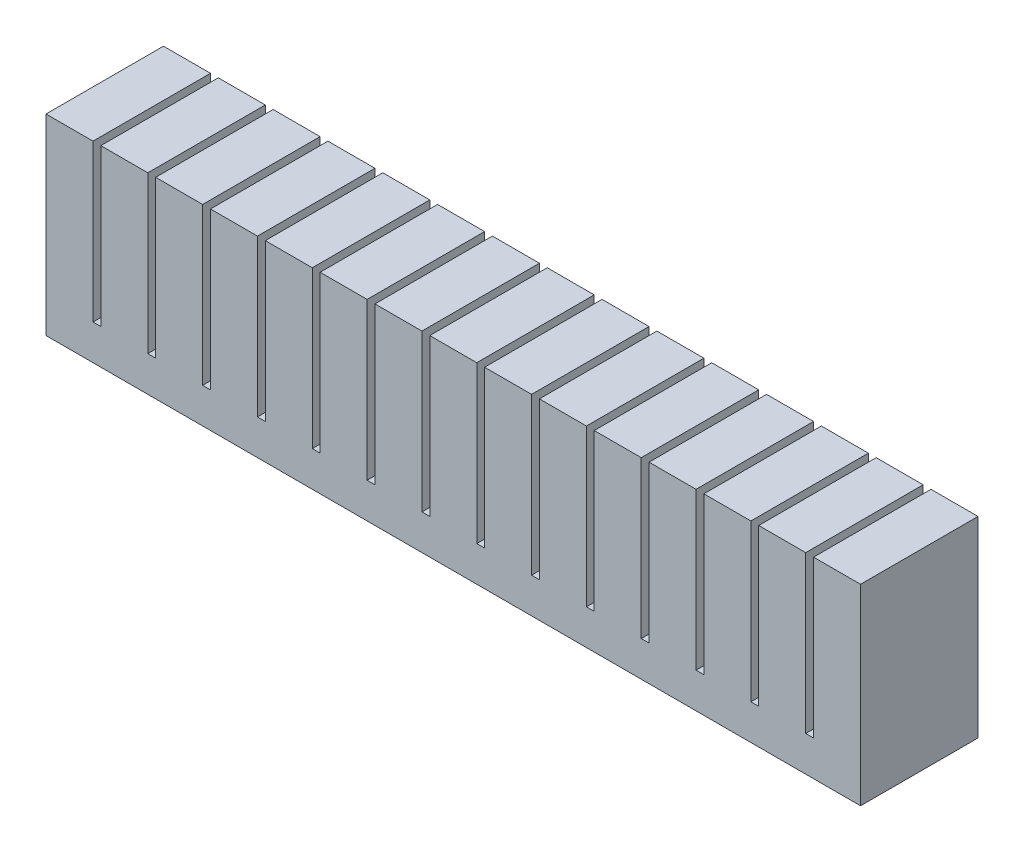
SolidWorks part; units mm, degrees
ref_plane "Front Plane" through (0, 0, 0) normal (0, 0, 1) x (1, 0, 0)
ref_plane "Top Plane" through (0, 0, 0) normal (0, 1, 0) x (1, 0, 0)
ref_plane "Right Plane" through (0, 0, 0) normal (1, 0, 0) x (0, 0, -1)
sketch "Sketch1" plane through (0, 0, 0) normal (0, 0, 1) x (1, 0, 0)
  line L0 (0, 0) -> (-3.5, 0)
  line L1 (-3.5, 0) -> (-3.5, 4.5)
  line L2 (-3.5, 4.5) -> (-3, 4.5)
  line L3 (-3, 4.5) -> (-3, 22.5)
  line L4 (-3, 22.5) -> (3, 22.5)
  line L5 (3, 22.5) -> (3, 4.5)
  line L6 (3, 4.5) -> (3.5, 4.5)
  line L7 (3.5, 4.5) -> (3.5, 0)
  line L8 (3.5, 0) -> (0, 0)
  point P12 (0, 22.5)
  dimension "D1" = 22.5
  dimension "D2" = 18
  dimension "D3" = 18
  dimension "D4" = 0.5
  dimension "D5" = 0.5
  dimension "D6" = 6
extrude "Boss-Extrude1" add sketch "Sketch1" along normal mid plane 15
pattern_linear "LPattern1" count 8 spacing 7 along (1, 0, 0) count 8 spacing 7 along (-1, 0, 0) of "Boss-Extrude1"
shell "Shell2" thickness 1
sketch "Sketch3" plane through (0, 0, 0) normal (0, 0, 1) x (1, 0, 0)
  line L0 (-52, 4.5) -> (-52.5, 4.5)
  line L1 (-52.5, 4.5) -> (-52.5, 0)
  line L2 (-52.5, 0) -> (52.5, 0) construction
  line L3 (-52.5, 4.5) -> (-52.5, 0) construction
  line L4 (-52.5, 0) -> (-52, 0)
  line L5 (-52, 0) -> (-52, 4.5)
  line L6 (52, 4.5) -> (52, 0)
  line L7 (52, 0) -> (52.5, 0)
  line L8 (52.5, 0) -> (52.5, 4.5)
  line L9 (52.5, 4.5) -> (52, 4.5)
extrude "Cut-Extrude2" cut sketch "Sketch3" along normal blind 15 and the other way through all
sketch "Sketch7" plane through (-52, 0, 0) normal (-1, 0, 0) x (0, 0, 1)
  line L0 (7.5, 22.5) -> (7.5, 0) construction
  line L1 (0, 0) -> (7.5, 0)
  line L2 (0, 0) -> (0, 1)
  line L3 (0, 1) -> (7.5, 1)
  line L4 (7.5, 0) -> (7.5, 1)
  dimension "D1" = 1
extrude "Cut-Extrude3" [suppressed] cut sketch "Sketch7" against normal through all
sketch "Sketch4" plane through (-52, 0, 0) normal (-1, 0, 0) x (0, 0, 1)
  line L1 (-6.5, 3.5) -> (6.5, 3.5)
  line L2 (-6.5, 3.5) -> (-6.5, 1)
  line L3 (-6.5, 1) -> (6.5, 1)
  line L4 (6.5, 3.5) -> (6.5, 1)
extrude "Boss-Extrude2" add sketch "Sketch4" against normal blind 1
sketch "Sketch5" plane through (52, 0, 0) normal (1, 0, 0) x (0, 0, -1)
  line L0 (6.5, 1) -> (6.5, 3.5) construction
  line L1 (-6.5, 3.5) -> (6.5, 3.5)
  line L2 (-6.5, 3.5) -> (-6.5, 1)
  line L3 (-6.5, 1) -> (6.5, 1)
  line L4 (6.5, 3.5) -> (6.5, 1)
  line L5 (6.5, 21.5) -> (6.5, 1) construction
extrude "Boss-Extrude3" add sketch "Sketch5" against normal blind 1
sketch "Sketch6" plane through (0, 0, 0) normal (0, 0, 1) x (1, 0, 0)
  line L0 (-52, 0) -> (52, 0)
  line L1 (52, 0) -> (52, -3.5)
  line L2 (52, -3.5) -> (-52, -3.5)
  line L3 (-52, -3.5) -> (-52, 0)
  dimension "D1" = 3.5
extrude "Boss-Extrude4" [suppressed] add sketch "Sketch6" along normal blind 15
sketch "Sketch8" plane through (0, 22.5, 0) normal (0, 1, 0) x (1, 0, 0)
  line L1 (-52, 7.5) -> (-46, 7.5)
  line L2 (-52, 7.5) -> (-52, -7.5)
  line L3 (-52, -7.5) -> (-46, -7.5)
  line L4 (-46, 7.5) -> (-46, -7.5)
extrude "Boss-Extrude5" add sketch "Sketch8" along normal blind 2
pattern_linear "LPattern2" count 15 spacing 7 along (1, 0, 0) of "Boss-Extrude5"
